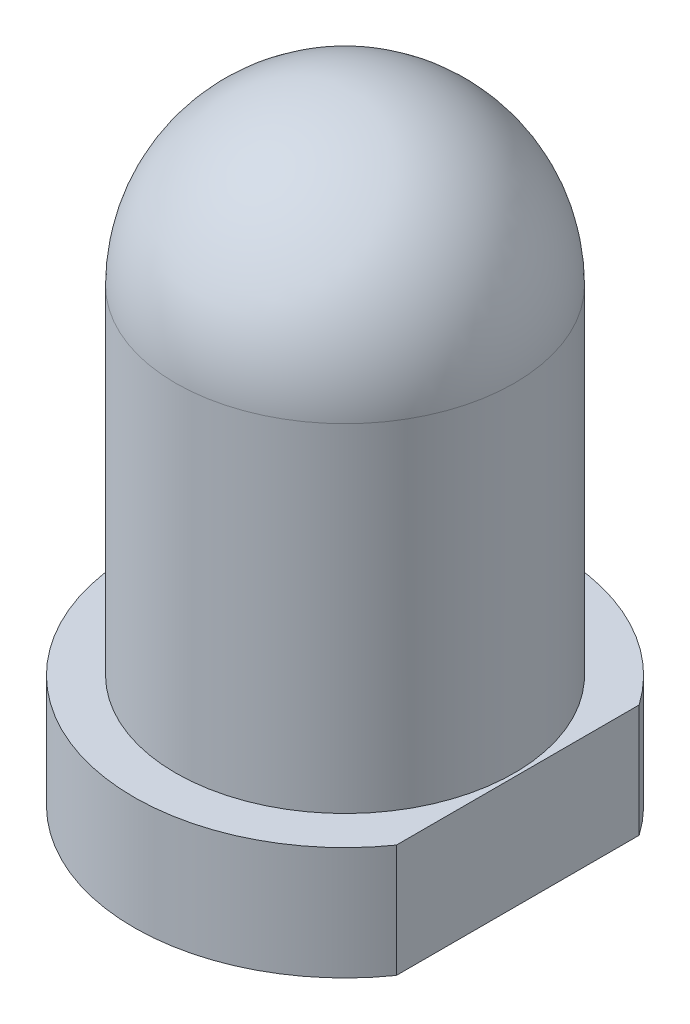
SolidWorks part; units mm, degrees
material "Epoxy, Unfilled"
ref_plane "Front Plane" through (0, 0, 0) normal (0, 0, 1) x (1, 0, 0)
ref_plane "Top Plane" through (0, 0, 0) normal (0, 1, 0) x (1, 0, 0)
ref_plane "Right Plane" through (0, 0, 0) normal (1, 0, 0) x (0, 0, -1)
sketch "Sketch1" plane through (0, 0, 0) normal (0, 1, 0) x (1, 0, 0)
  circle A0 centre (0, 0) radius 1.87
  dimension "D1" = 3.74
extrude "Boss-Extrude1" add sketch "Sketch1" along normal blind 1
sketch "Sketch3" plane through (0, 0, 0) normal (0, 0, 1) x (1, 0, 0)
  line L0 (0, 5.49) -> (0, 3.99) construction
  line L1 (0, 5.49) -> (0, 1) construction
  line L2 (1.87, 1) -> (-1.87, 1) construction
  line L3 (1.5, 3.99) -> (1.5, 1)
  line L4 (1.5, 1) -> (0, 1)
  line L5 (0, 5.49) -> (0, 1)
  arc A0 (1.5, 3.99) -> (0, 5.49) centre (0, 3.99) ccw
  dimension "D1" = 4.49
  dimension "D2" = 1.5
revolve "Revolve2" add sketch "Sketch3" angle 360 about L5
sketch "Sketch6" plane through (0, 1, 0) normal (0, 1, 0) x (1, 0, 0)
  line L1 (1.53, 1.5072) -> (2.21, 1.5072)
  line L2 (1.53, 1.5072) -> (1.53, -1.5072)
  line L3 (1.53, -1.5072) -> (2.21, -1.5072)
  line L4 (2.21, 1.5072) -> (2.21, -1.5072)
  line L5 (1.53, 1.5072) -> (2.21, -1.5072) construction
  line L6 (1.53, -1.5072) -> (2.21, 1.5072) construction
  circle A0 centre (0, 0) radius 1.87 construction
  point P0 (1.87, 0)
extrude "Cut-Extrude1" cut sketch "Sketch6" against normal blind 1
